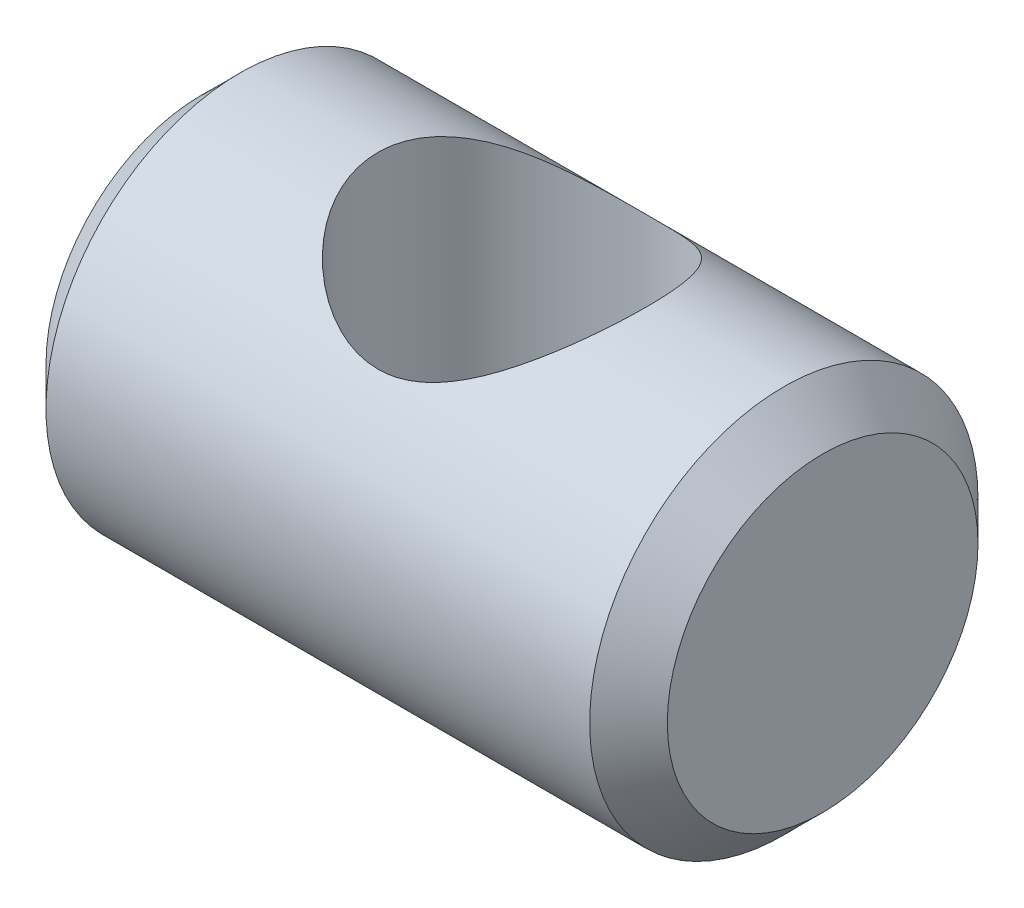
SolidWorks part; units mm, degrees
ref_plane "Front Plane" through (0, 0, 0) normal (0, 0, 1) x (1, 0, 0)
ref_plane "Top Plane" through (0, 0, 0) normal (0, 1, 0) x (1, 0, 0)
ref_plane "Right Plane" through (0, 0, 0) normal (1, 0, 0) x (0, 0, -1)
sketch "Sketch1" plane through (0, 0, 0) normal (1, 0, 0) x (0, 0, -1)
  circle A0 centre (0, 0) radius 5
  dimension "D1" = 10
extrude "Boss-Extrude1" add sketch "Sketch1" along normal blind 16
sketch "Sketch2" plane through (0, 0, 0) normal (0, 1, 0) x (1, 0, 0)
  line L0 (0, 0) -> (8, 0) construction
  circle A0 centre (8, 0) radius 3.4532
  dimension "D1" = 8
extrude "Cut-Extrude1" cut sketch "Sketch2" against normal through all both and the other way through all
chamfer "Chamfer1" distance 1 angle 45 2 edges at (16, 0, -5) (0, 0, -5)
